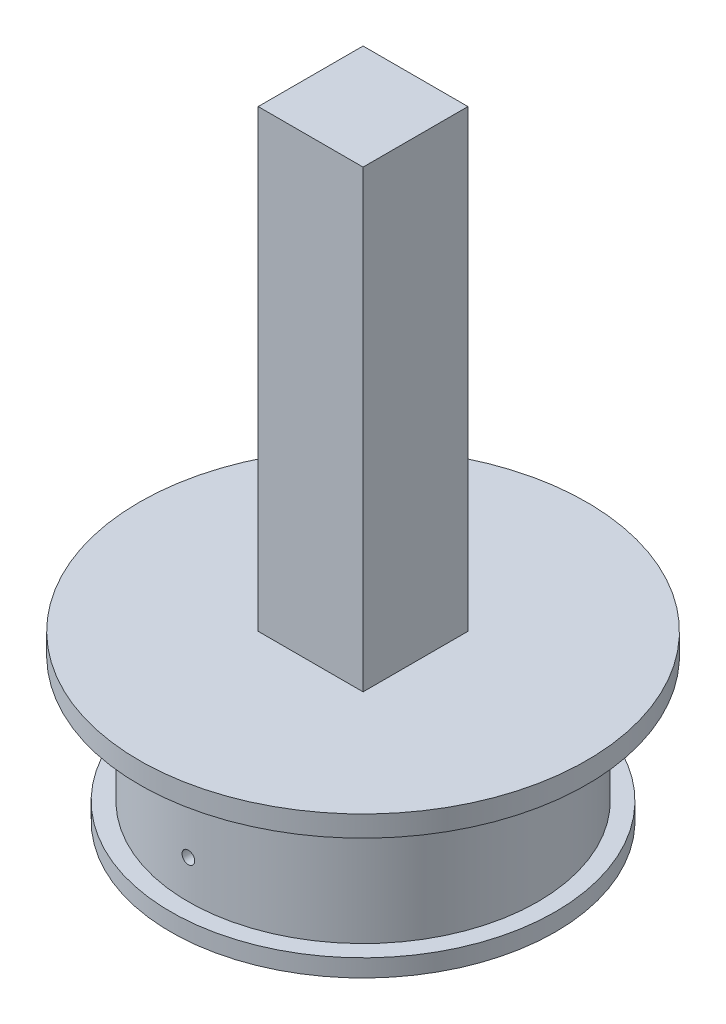
SolidWorks part; units mm, degrees
ref_plane "Front Plane" through (0, 0, 0) normal (0, 0, 1) x (1, 0, 0)
ref_plane "Top Plane" through (0, 0, 0) normal (0, 1, 0) x (1, 0, 0)
ref_plane "Right Plane" through (0, 0, 0) normal (1, 0, 0) x (0, 0, -1)
sketch "Sketch2" plane through (0, 0, 0) normal (0, 0, 1) x (1, 0, 0)
  line L0 (373.8696, 178.0063) -> (373.8696, 103.3422)
  line L1 (363.8696, 178.0063) -> (363.8696, 173.0063)
  line L2 (363.8696, 178.0063) -> (373.8696, 178.0063)
  line L3 (363.8696, 173.0063) -> (373.8696, 173.0063)
  line L4 (373.8696, 178.0063) -> (373.8696, 173.0063)
  line L5 (363.8696, 108.3422) -> (363.8696, 103.3422)
  line L6 (363.8696, 108.3422) -> (373.8696, 108.3422)
  line L7 (363.8696, 103.3422) -> (373.8696, 103.3422)
  line L8 (373.8696, 108.3422) -> (373.8696, 103.3422)
  line L9 (373.8696, 178.0063) -> (378.8696, 178.0063)
  line L10 (373.8696, 103.3422) -> (378.8696, 103.3422)
  line L11 (378.8696, 178.0063) -> (378.8696, 103.3422)
  circle A0 centre (366.3696, 105.8422) radius 1.15
  circle A2 centre (366.3696, 175.5063) radius 1.15
  dimension "D3" = 2.3
  dimension "D7" = 2.5
  dimension "D4" = 2.3
  dimension "D9" = 2.5
  dimension "D1" = 5
  dimension "D2" = 5
  dimension "D5" = 10
  dimension "D6" = 10
  dimension "D8" = 5
extrude "Boss-Extrude1" add sketch "Sketch2" along normal blind 1.5 contours L11 L9 L0 L10 | L1 L3 L0 L2 A2 | L5 L7 L0 L6 A0
sketch "Sketch3" plane through (378.8696, 0, 0) normal (1, 0, 0) x (0, 0, -1)
  line L0 (-1.5, 178.0063) -> (-1.5, 103.3422)
  line L1 (-1.5, 178.0063) -> (11.5, 178.0063)
  line L2 (-1.5, 103.3422) -> (11.5, 103.3422)
  line L3 (11.5, 178.0063) -> (11.5, 103.3422)
  dimension "D1" = 13
extrude "Boss-Extrude2" add sketch "Sketch3" along normal blind 1
ref_plane "Plane2" through (0, 0, -5) normal (0, 0, -1) x (-1, 0, 0)
mirror "Mirror3" about plane through (0, 0, -5) normal (0, 0, -1) of "Boss-Extrude1"
move or copy body "Body-Move/Copy1" bodies to move or copy 105 copy yes number of copies 1 translate (0, 0, 84.96)
sketch "Sketch5" plane through (379.8696, 0, 0) normal (1, 0, 0) x (0, 0, -1)
  line L0 (-86.46, 178.0063) -> (11.5, 178.0063)
  line L1 (-86.46, 178.0063) -> (-86.46, 103.3576)
  line L2 (11.5, 178.0063) -> (11.5, 103.3576)
  line L3 (-86.46, 103.3576) -> (11.5, 103.3576)
extrude "Boss-Extrude3" add sketch "Sketch5" against normal up to surface (1 mm away)
sketch "Sketch6" plane through (378.8696, 0, 0) normal (-1, 0, 0) x (0, 0, 1)
  circle A0 centre (37.48, 140.6743) radius 25
  circle A1 centre (37.48, 140.6743) radius 23
  dimension "D1" = 50
  dimension "D2" = 2
extrude "Boss-Extrude4" add sketch "Sketch6" along normal blind 18
sketch "Sketch8" plane through (360.8696, 0, 0) normal (-1, 0, 0) x (0, 0, 1)
  circle A0 centre (37.48, 140.6743) radius 23.5
  circle A1 centre (37.48, 140.6743) radius 27.5
  dimension "D1" = 55
  dimension "D2" = 4
extrude "Boss-Extrude6" add sketch "Sketch8" along normal blind 2.5
ref_plane "Plane3" through (0, 140.6743, 0) normal (0, 1, 0) x (1, 0, 0)
ref_plane "Plane5" through (0, 0, 37.48) normal (0, 0, 1) x (1, 0, 0)
sketch "Sketch13" plane through (378.8696, 0, 0) normal (-1, 0, 0) x (0, 0, 1)
  line L0 (1.5, 178.0063) -> (73.46, 178.0063) construction
  line L1 (28.48, 178.0063) -> (46.48, 178.0063)
  line L2 (28.48, 178.0063) -> (28.48, 201.0063)
  line L3 (28.48, 201.0063) -> (46.48, 201.0063)
  line L4 (46.48, 178.0063) -> (46.48, 201.0063)
  line L10 (37.48, -55) -> (37.48, 55) construction
  line L11 (73.46, 103.3576) -> (1.5, 103.3576) construction
  line L12 (46.48, 103.3576) -> (28.48, 103.3576)
  line L13 (46.48, 103.3576) -> (46.48, 80.3576)
  line L14 (46.48, 80.3576) -> (28.48, 80.3576)
  line L15 (28.48, 103.3576) -> (28.48, 80.3576)
  dimension "D1" = 9
  dimension "D2" = 9
  dimension "D3" = 23
  dimension "D4" = 23
  dimension "D5" = 0
  dimension "D6" = 0
extrude "Boss-Extrude7" add sketch "Sketch13" against normal blind 1
sketch "Sketch15" plane through (378.8696, 0, 0) normal (-1, 0, 0) x (0, 0, 1)
  line L0 (37.48, -55) -> (37.48, 55) construction
  line L1 (28.48, 80.3576) -> (46.48, 80.3576) construction
  line L2 (46.48, 201.0063) -> (28.48, 201.0063) construction
  circle A0 centre (37.48, 195.0063) radius 3.75
  circle A1 centre (37.48, 86.3576) radius 3.75
  dimension "D1" = 7.5
  dimension "D2" = 7.5
  dimension "D3" = 6
  dimension "D4" = 6
extrude "Cut-Extrude3" cut sketch "Sketch15" against normal blind 1
move or copy body "Body-Move/Copy2" bodies to move or copy 116 copy no rotation origin (371.8696, 140.6819, 0) rotation axis (0, 0, 1) rotation angle 90
sketch "Sketch16" plane through (0, 148.6819, 0) normal (0, 1, 0) x (1, 0, 0)
  line L0 (334.5452, -28.48) -> (334.5452, 11.5)
  line L1 (311.5452, -28.48) -> (334.5452, -28.48)
  line L2 (311.5452, -28.48) -> (311.5452, -46.48)
  line L3 (311.5452, -46.48) -> (334.5452, -46.48)
  line L5 (432.194, -28.48) -> (409.194, -28.48)
  line L6 (432.194, -28.48) -> (432.194, -46.48)
  line L7 (432.194, -46.48) -> (409.194, -46.48)
  line L9 (334.5452, 11.5) -> (409.2093, 11.5)
  line L10 (409.2093, 11.5) -> (409.194, -28.48)
  line L11 (409.194, -46.48) -> (409.2093, -86.46)
  line L12 (409.2093, -86.46) -> (334.5452, -86.46)
  line L13 (334.5452, -86.46) -> (334.5452, -46.48)
  circle A0 centre (317.5452, -37.48) radius 3.75
  circle A1 centre (426.194, -37.48) radius 3.75
extrude "Boss-Extrude8" add sketch "Sketch16" along normal blind 6
sketch "Sketch17" plane through (0, 0, 37.48) normal (0, 0, 1) x (1, 0, 0)
  line L0 (344.3772, 127.1819) -> (399.3772, 127.1819) construction
  circle A0 centre (371.8772, 135.1819) radius 0.9
  dimension "D1" = 1.8
  dimension "D2" = 8
extrude "Cut-Extrude4" cut sketch "Sketch17" against normal blind 44 and the other way blind 46
sketch "Sketch18" plane through (0, 154.6819, 0) normal (0, 1, 0) x (1, 0, 0)
  line L1 (297.382, 14.9684) -> (439.9066, 14.9684)
  line L2 (297.382, 14.9684) -> (297.382, -97.1468)
  line L3 (297.382, -97.1468) -> (439.9066, -97.1468)
  line L4 (439.9066, 14.9684) -> (439.9066, -97.1468)
extrude "Cut-Extrude5" cut sketch "Sketch18" against normal up to surface (7 mm away) up to face at (371.8772, 147.6819, 79.96)
sketch "Sketch20" plane through (0, 147.6819, 0) normal (0, 1, 0) x (1, 0, 0)
  circle A0 centre (371.8772, -37.48) radius 32
  circle A1 centre (371.8772, -37.48) radius 25 construction
  dimension "D1" = 7
extrude "Boss-Extrude9" add sketch "Sketch20" along normal blind 3
sketch "Sketch22" plane through (0, 150.6819, 0) normal (0, 1, 0) x (1, 0, 0)
  circle A0 centre (371.8772, -37.48) radius 7.553
sketch "Sketch23" plane through (0, 150.6819, 0) normal (0, 1, 0) x (1, 0, 0)
  line L1 (364.3772, -29.98) -> (379.3772, -29.98)
  line L2 (364.3772, -29.98) -> (364.3772, -44.98)
  line L3 (364.3772, -44.98) -> (379.3772, -44.98)
  line L4 (379.3772, -29.98) -> (379.3772, -44.98)
  line L5 (364.3772, -29.98) -> (379.3772, -44.98) construction
  line L6 (364.3772, -44.98) -> (379.3772, -29.98) construction
  point P0 (371.8772, -37.48)
  dimension "D1" = 15
  dimension "D2" = 15
extrude "Boss-Extrude11" add sketch "Sketch23" along normal blind 65
